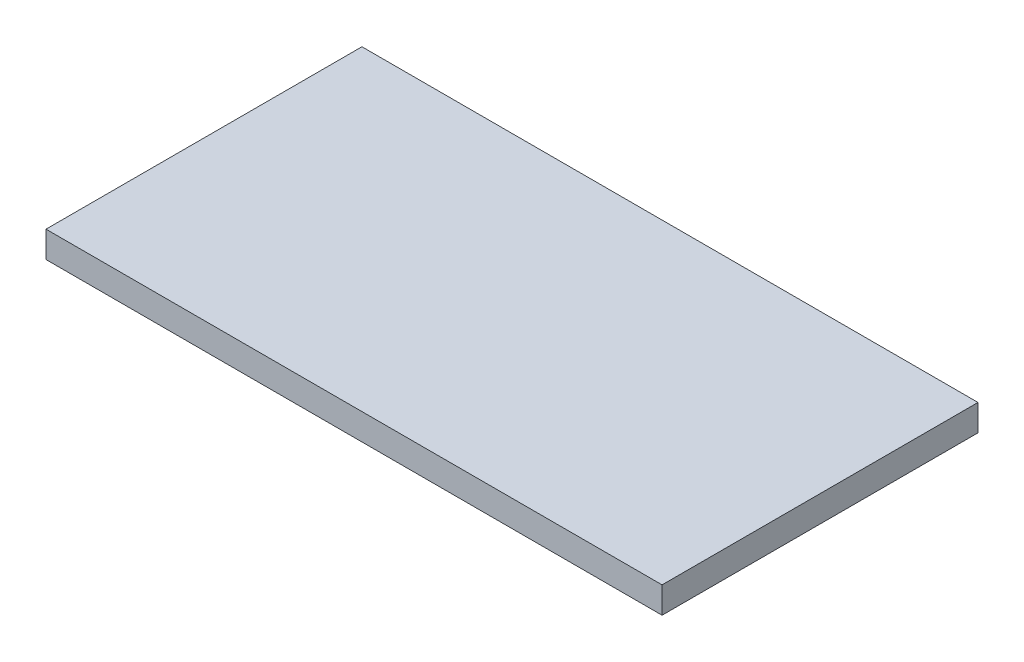
SolidWorks part; units mm, degrees
ref_plane "Front" through (0, 0, 0) normal (0, 0, 1) x (1, 0, 0)
ref_plane "Top" through (0, 0, 0) normal (0, 1, 0) x (1, 0, 0)
ref_plane "Right" through (0, 0, 0) normal (1, 0, 0) x (0, 0, -1)
sketch "Sketch1" plane through (0, 0, 0) normal (0, 1, 0) x (1, 0, 0)
  line L1 (-58.5, -30) -> (58.5, -30)
  line L2 (-58.5, -30) -> (-58.5, 30)
  line L3 (-58.5, 30) -> (58.5, 30)
  line L4 (58.5, -30) -> (58.5, 30)
  line L5 (-58.5, -30) -> (58.5, 30) construction
  line L6 (-58.5, 30) -> (58.5, -30) construction
  line L67 (-58.5, -30) -> (58.5, -30)
  point P0 (0, 0)
  dimension "D1" = 117
  dimension "D2" = 60
extrude "Boss-Extrude1" add sketch "Sketch1" along normal blind 5
